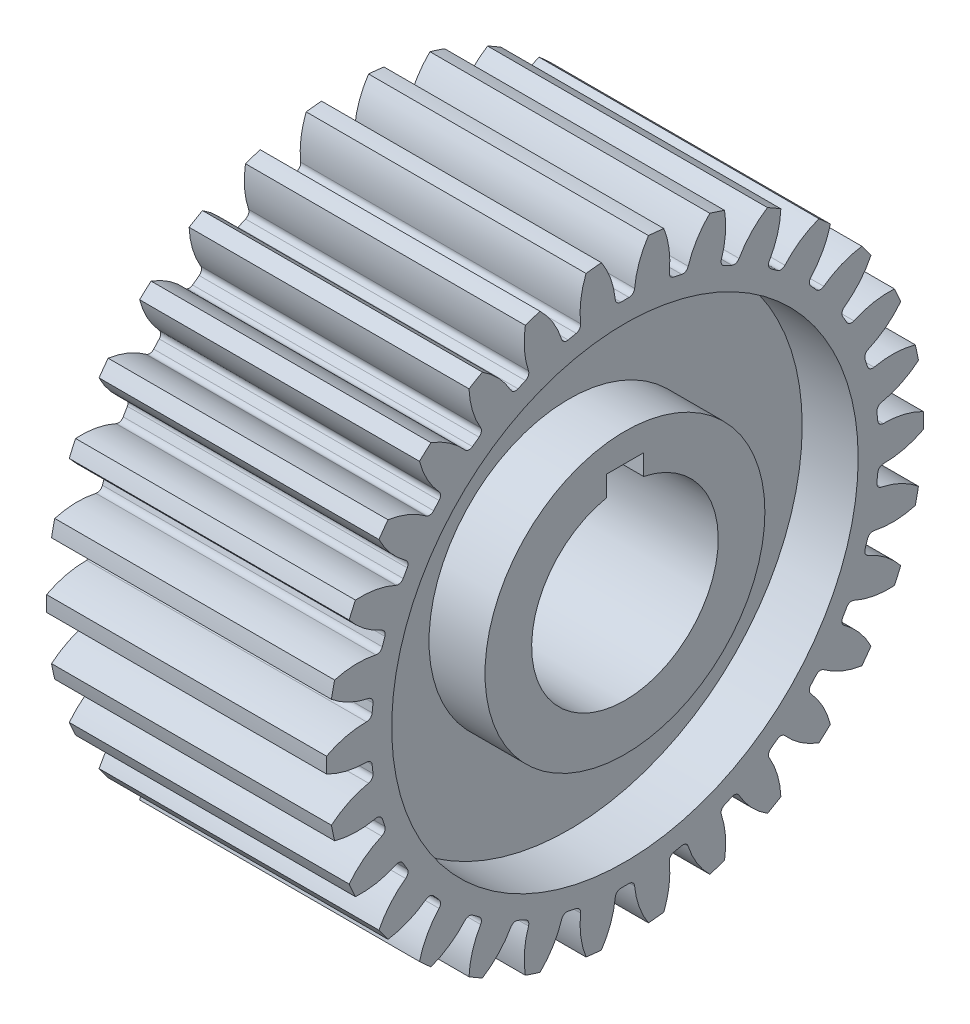
SolidWorks part; units mm, degrees
ref_plane "Front Plane" through (0, 0, 0) normal (0, 0, 1) x (1, 0, 0)
ref_plane "Top Plane" through (0, 0, 0) normal (0, 1, 0) x (1, 0, 0)
ref_plane "Right Plane" through (0, 0, 0) normal (1, 0, 0) x (0, 0, -1)
sketch "Sketch1" plane through (0, 0, 0) normal (1, 0, 0) x (0, 0, -1)
  circle A0 centre (0, 0) radius 16
  dimension "D1" = 32
extrude "Boss-Extrude1" add sketch "Sketch1" along normal mid plane 15
sketch "Sketch4" plane through (7.5, 0, 0) normal (1, 0, 0) x (0, 0, -1)
  line L1 (-1, 6) -> (1, 6)
  line L2 (-1, 6) -> (-1, 4.899)
  line L4 (1, 6) -> (1, 4.899)
  line L5 (-1, 6) -> (1, 4) construction
  line L6 (-1, 4) -> (1, 6) construction
  arc A0 (-1, 4.899) -> (1, 4.899) centre (0, 0) ccw
  point P3 (0, 5)
  dimension "D1" = 10
  dimension "D2" = 2
  dimension "D3" = 2
extrude "Cut-Extrude1" cut sketch "Sketch4" against normal through all
sketch "Sketch5" plane through (7.5, 0, 0) normal (1, 0, 0) x (0, 0, -1)
  circle A0 centre (0, 0) radius 7.5
  circle A1 centre (0, 0) radius 12.5
  dimension "D1" = 25
  dimension "D2" = 15
extrude "Cut-Extrude2" cut sketch "Sketch5" against normal blind 3
mirror "Mirror2" about plane through (0, 0, 0) normal (1, 0, 0) of "Cut-Extrude2"
sketch "Sketch9" plane through (7.5, 0, 0) normal (1, 0, 0) x (0, 0, -1)
  line L0 (0, 0) -> (0, 24.3135) construction
  line L1 (-0.2199, 13.6) -> (0.2199, 13.6)
  arc A0 (0.5184, 13.8707) -> (2.08, 16.88) centre (5.0567, 13.4256) cw
  arc A3 (-0.5184, 13.8707) -> (-2.08, 16.88) centre (-5.0567, 13.4256) ccw
  arc A4 (-2.08, 16.88) -> (2.08, 16.88) centre (0, -0.9994) cw
  arc A5 (0.2199, 13.6) -> (0.5184, 13.8707) centre (0.2199, 13.9) ccw
  arc A6 (-0.5184, 13.8707) -> (-0.2199, 13.6) centre (-0.2199, 13.9) ccw
  point P8 (0, 13.6)
  point P13 (0.5, 13.6)
  point P16 (-0.5, 13.6)
  dimension "D4" = 3.28
  dimension "D5" = 4.56
  dimension "D6" = 18
  dimension "D7" = 0.3
  dimension "D1" = 0.5
  dimension "D2" = 13.6
  dimension "D3" = 1.58
extrude "Cut-Extrude7" cut sketch "Sketch9" against normal through all
pattern_circular "CirPattern1" count 30 over 360 about axis through (0, 0, 0) along (1, 0, 0) of "Cut-Extrude7"
